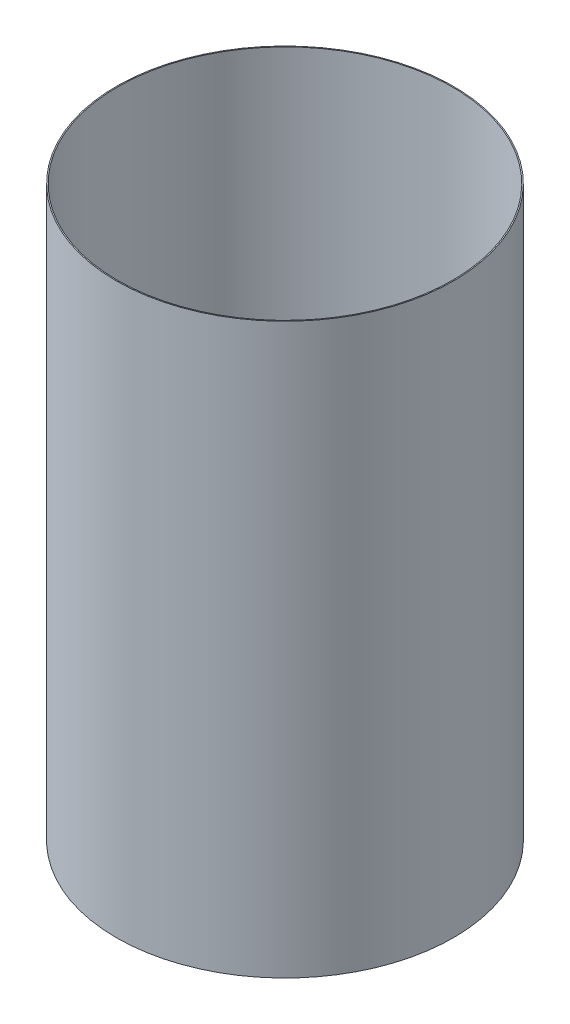
SolidWorks part; units mm, degrees
material "Thornel Mat VMA"
ref_plane "Front Plane" through (0, 0, 0) normal (0, 0, 1) x (1, 0, 0)
ref_plane "Top Plane" through (0, 0, 0) normal (0, 1, 0) x (1, 0, 0)
ref_plane "Right Plane" through (0, 0, 0) normal (1, 0, 0) x (0, 0, -1)
ref_axis "Axis1" through (0, 55, 0) along (0, -1, 0)
sketch "Sketch1" plane through (0, 0, 0) normal (0, 0, 1) x (1, 0, 0)
  line L0 (-39.2684, -69.0032) -> (-39.2684, -202.3532)
  line L2 (-38.1, -202.3532) -> (0, -202.3532) construction
  line L3 (-38.1, -69.0032) -> (0, -69.0032) construction
revolve "Revolve-Thin1" add sketch "Sketch1" angle 360 about axis through (0, 55, 0) along (0, -1, 0)
equation "\"D3@Revolve-Thin1\"=\"CF THICKNESS@Cryo Tank.Assembly\""
